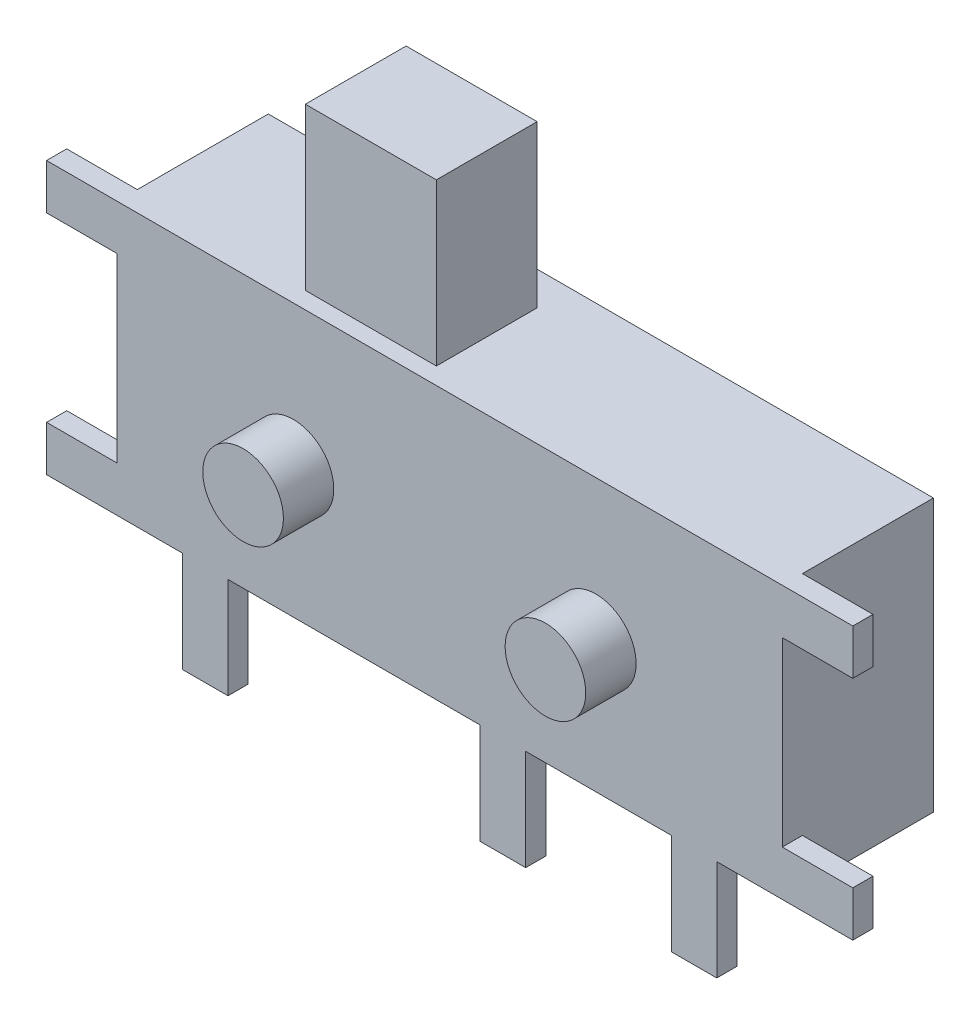
SolidWorks part; units mm, degrees
ref_plane "前视基准面" through (0, 0, 0) normal (0, 0, 1) x (1, 0, 0)
ref_plane "上视基准面" through (0, 0, 0) normal (0, 1, 0) x (1, 0, 0)
ref_plane "右视基准面" through (0, 0, 0) normal (1, 0, 0) x (0, 0, -1)
sketch "草图1" plane through (0, 0, 0) normal (0, 0, 1) x (1, 0, 0)
  line L1 (-3.3, -1.35) -> (3.3, -1.35)
  line L2 (-3.3, -1.35) -> (-3.3, 1.35)
  line L3 (-3.3, 1.35) -> (3.3, 1.35)
  line L4 (3.3, -1.35) -> (3.3, 1.35)
  line L5 (-3.3, -1.35) -> (3.3, 1.35) construction
  line L6 (-3.3, 1.35) -> (3.3, -1.35) construction
  point P0 (0, 0)
  dimension "D1" = 6.6
  dimension "D2" = 2.7
extrude "凸台-拉伸1" add sketch "草图1" against normal blind 1.5
sketch "草图2" plane through (0, 0, 0) normal (0, 0, 1) x (1, 0, 0)
  line L0 (-3.3, 1.35) -> (-3.3, -1.35) construction
  line L4 (3.3, -1.35) -> (3.3, 1.35)
  line L5 (3.3, 1.35) -> (-3.3, 1.35)
  line L6 (-3.3, 1.35) -> (-3.3, -1.35)
  line L7 (-3.3, -1.35) -> (3.3, -1.35)
  line L8 (3.3, -1.35) -> (3.3, 1.35) construction
  line L9 (3.3, 1.35) -> (-3.3, 1.35) construction
  line L10 (-3.3, 1.35) -> (-3.3, -1.35) construction
  line L11 (-3.3, -1.35) -> (3.3, -1.35) construction
  line L13 (-3.3, 1.35) -> (-4, 1.35)
  line L14 (-3.3, 1.35) -> (-3.3, 0.9)
  line L15 (-3.3, 0.9) -> (-4, 0.9)
  line L16 (-4, 1.35) -> (-4, 0.9)
  line L17 (0, 0) -> (-1.3732, 0) construction
  line L18 (0, 0) -> (0, 0.5144) construction
  line L19 (4, 1.35) -> (4, 0.9)
  line L20 (3.3, 0.9) -> (4, 0.9)
  line L21 (3.3, 1.35) -> (3.3, 0.9)
  line L22 (3.3, 1.35) -> (4, 1.35)
  line L23 (3.3, -1.35) -> (4, -1.35)
  line L24 (3.3, -1.35) -> (3.3, -0.9)
  line L25 (3.3, -0.9) -> (4, -0.9)
  line L26 (4, -1.35) -> (4, -0.9)
  line L27 (-4, -1.35) -> (-4, -0.9)
  line L28 (-3.3, -0.9) -> (-4, -0.9)
  line L29 (-3.3, -1.35) -> (-3.3, -0.9)
  line L30 (-3.3, -1.35) -> (-4, -1.35)
  dimension "D2" = 0.7
  dimension "D3" = 0.45
  dimension "D1" = 0
extrude "外壳固定引脚" add sketch "草图2" against normal blind 0.2
sketch "草图3" plane through (0, 0, 0) normal (0, 0, 1) x (1, 0, 0)
  line L0 (-4, -1.35) -> (4, -1.35) construction
  line L1 (2.65, -1.35) -> (2.2, -1.35)
  line L2 (2.65, -1.35) -> (2.65, -2.35)
  line L3 (2.65, -2.35) -> (2.2, -2.35)
  line L4 (2.2, -1.35) -> (2.2, -2.35)
  line L5 (3.3, -0.9) -> (3.3, 0.9) construction
  line L6 (0, 0) -> (0, -1.7018) construction
  line L7 (-2.2, -1.35) -> (-2.2, -2.35)
  line L8 (-2.65, -2.35) -> (-2.2, -2.35)
  line L9 (-2.65, -1.35) -> (-2.65, -2.35)
  line L10 (-2.65, -1.35) -> (-2.2, -1.35)
  line L12 (0.754, -1.35) -> (0.3, -1.35)
  line L13 (0.754, -1.35) -> (0.754, -2.35)
  line L14 (0.754, -2.35) -> (0.3, -2.35)
  line L15 (0.3, -1.35) -> (0.3, -2.35)
  dimension "D1" = 1.1
  dimension "D2" = 0.45
  dimension "D3" = 1
  dimension "D4" = 1.9
  dimension "D5" = 0.454
  dimension "D6" = 1
extrude "有用的引脚" add sketch "草图3" against normal blind 0.2
sketch "草图4" plane through (0, 1.35, 0) normal (0, 1, 0) x (1, 0, 0)
  line L1 (-1.6, 1.1677) -> (-0.3, 1.1677)
  line L2 (-1.6, 1.1677) -> (-1.6, 0.1677)
  line L3 (-1.6, 0.1677) -> (-0.3, 0.1677)
  line L4 (-0.3, 1.1677) -> (-0.3, 0.1677)
  line L5 (-3.3, 1.5) -> (-3.3, 0.2) construction
  dimension "D1" = 3
  dimension "D2" = 1.3
  dimension "D3" = 1
extrude "凸台-拉伸4" add sketch "草图4" along normal blind 1.6
sketch "草图5" plane through (0, 0, 0) normal (0, 0, 1) x (1, 0, 0)
  line L0 (3.3, -0.9) -> (3.3, 0.9) construction
  line L2 (0.754, -1.35) -> (2.2, -1.35) construction
  circle A0 centre (1.45, -0.05) radius 0.4
  circle A1 centre (-1.55, -0.05) radius 0.4
  dimension "D2" = 0.8
  dimension "D1" = 1.85
  dimension "D3" = 1.3
  dimension "D4" = 2
extrude "凸台-拉伸5" add sketch "草图5" along normal blind 0.5
sketch "草图6" plane through (0, 0, 0) normal (0, 0, 1) x (1, 0, 0)
  circle A0 centre (-1.55, -0.05) radius 0.4 construction
  circle A1 centre (-1.55, -0.05) radius 0.4
  circle A2 centre (1.45, -0.05) radius 0.4 construction
  circle A3 centre (1.45, -0.05) radius 0.4
